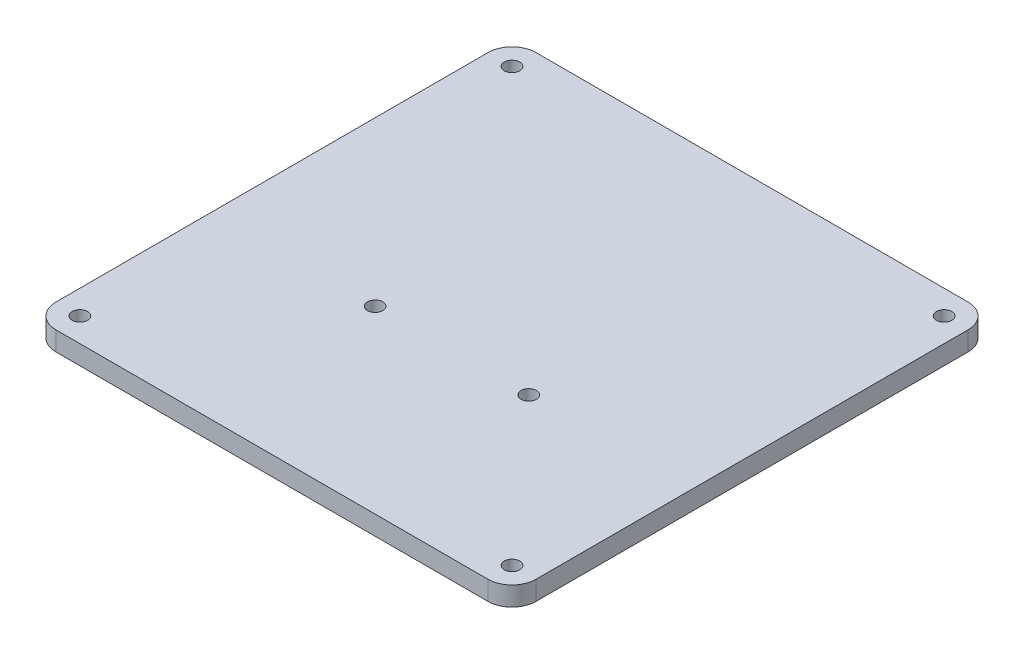
SolidWorks part; units mm, degrees
ref_plane "Front Plane" through (0, 0, 0) normal (0, 0, 1) x (1, 0, 0)
ref_plane "Top Plane" through (0, 0, 0) normal (0, 1, 0) x (1, 0, 0)
ref_plane "Right Plane" through (0, 0, 0) normal (1, 0, 0) x (0, 0, -1)
sketch "Sketch1" plane through (0, 0, 0) normal (0, 1, 0) x (1, 0, 0)
  line L1 (-45, -45) -> (45, -45) construction
  line L2 (-45, -45) -> (-45, 45) construction
  line L3 (-45, 45) -> (45, 45) construction
  line L4 (45, -45) -> (45, 45) construction
  line L5 (0, 45) -> (0, -45) construction
  line L6 (-45, 0) -> (45, 0) construction
  line L7 (50, -50) -> (-50, -50)
  line L8 (50, -50) -> (50, 50)
  line L9 (50, 50) -> (-50, 50)
  line L10 (-50, -50) -> (-50, 50)
  line L11 (0, 50) -> (0, -50) construction
  line L12 (50, 0) -> (-50, 0) construction
  circle A0 centre (-45, 45) radius 1.6
  circle A1 centre (45, 45) radius 1.6
  circle A2 centre (45, -45) radius 1.6
  circle A3 centre (-45, -45) radius 1.6
  circle A4 centre (16, -12.5) radius 1.6
  circle A5 centre (-16, -12.5) radius 1.6
  point P0 (0, 0)
  point P4 (0, 0)
  dimension "D5" = 3.2
  dimension "D6" = 32.5
  dimension "D1" = 90
  dimension "D2" = 90
  dimension "D3" = 100
  dimension "D4" = 100
  dimension "D7" = 29
extrude "Boss-Extrude1" add sketch "Sketch1" along normal blind 4
fillet "Fillet1" radius 5 4 edges at (-50, 2, -50) (50, 2, -50) (50, 2, 50) (-50, 2, 50)
